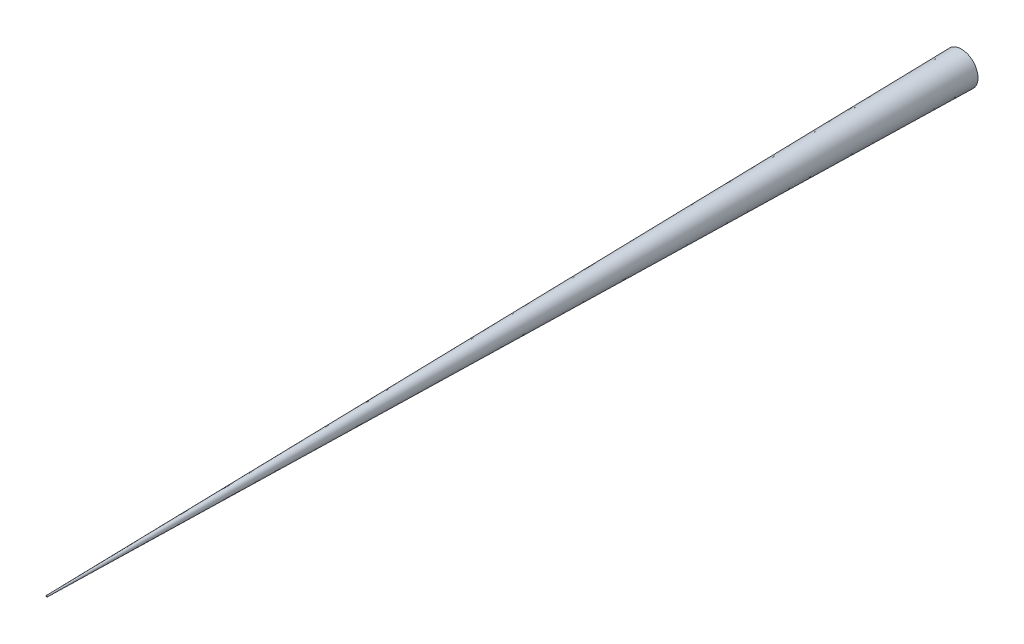
SolidWorks part; units mm, degrees
ref_plane "Front Plane" through (0, 0, 0) normal (0, 0, 1) x (1, 0, 0)
ref_plane "Top Plane" through (0, 0, 0) normal (0, 1, 0) x (1, 0, 0)
ref_plane "Right Plane" through (0, 0, 0) normal (1, 0, 0) x (0, 0, -1)
sketch "Sketch1" plane through (0, 0, 0) normal (0, 0, 1) x (1, 0, 0)
  circle A0 centre (0, 0) radius 12.7
  dimension "D1" = 25.4
extrude "Boss-Extrude2" add sketch "Sketch1" along normal blind 700 draft 1
